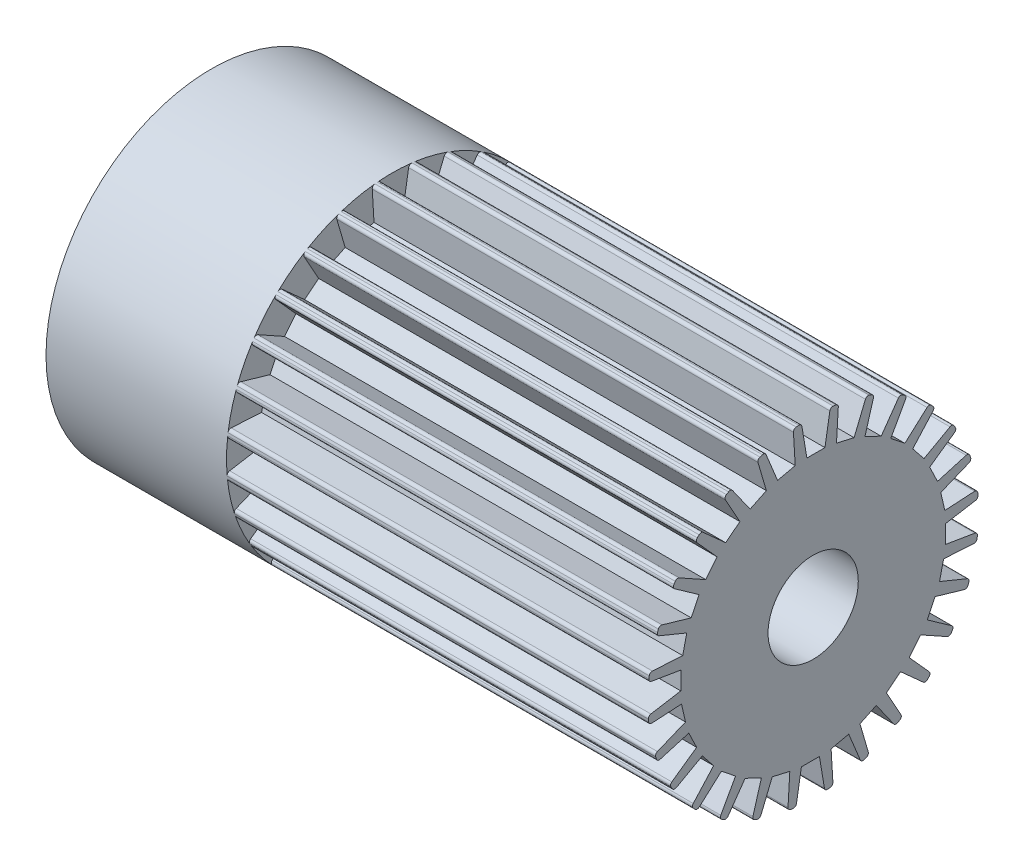
SolidWorks part; units mm, degrees
ref_plane "Front Plane" through (0, 0, 0) normal (0, 0, 1) x (1, 0, 0)
ref_plane "Top Plane" through (0, 0, 0) normal (0, 1, 0) x (1, 0, 0)
ref_plane "Right Plane" through (0, 0, 0) normal (1, 0, 0) x (0, 0, -1)
sketch "Sketch2" plane through (0, 0, 0) normal (0, 0, 1) x (1, 0, 0)
  line L0 (0, 0) -> (-6.3477, 0) construction
  line L1 (4.4247, 0.75) -> (-5.5753, 0.75)
  line L2 (-5.5753, 0.75) -> (-5.5753, 2.75)
  line L3 (-5.5753, 2.75) -> (4.4247, 2.75)
  line L4 (4.4247, 2.75) -> (4.4247, 0.75)
  dimension "D1" = 1.5
  dimension "D2" = 5.5
  dimension "D3" = 10
revolve "Revolve2" add sketch "Sketch2" angle 360 about L0
sketch "Sketch3" plane through (4.4247, 0, 0) normal (1, 0, 0) x (0, 0, -1)
  line L0 (-0.2041, 2.7996) -> (-0.1041, 2.1996)
  line L1 (0.1959, 2.1996) -> (0.2959, 2.7996)
  line L2 (0.2959, 2.7996) -> (-0.2041, 2.7996)
  line L3 (-0.1041, 2.1996) -> (0.1959, 2.1996)
  circle A0 centre (0, 0) radius 2.75 construction
  point P4 (0.0459, 2.7996)
  point P5 (0.0459, 2.1996)
  point P8 (0.0459, 2.7496)
  dimension "D1" = 0.3
  dimension "D2" = 0.5
  dimension "D3" = 0.6
  dimension "D4" = 0.55
extrude "Cut-Extrude1" cut sketch "Sketch3" against normal blind 7
fillet "Fillet1" radius 0.05 2 edges at (0.9247, 2.7431, 0.1947) (0.9247, 2.7352, -0.2851)
pattern_circular "CirPattern6" count 28 over 360 about axis through (0, 0, 0) along (1, 0, 0) of "Cut-Extrude1", "Fillet1"
